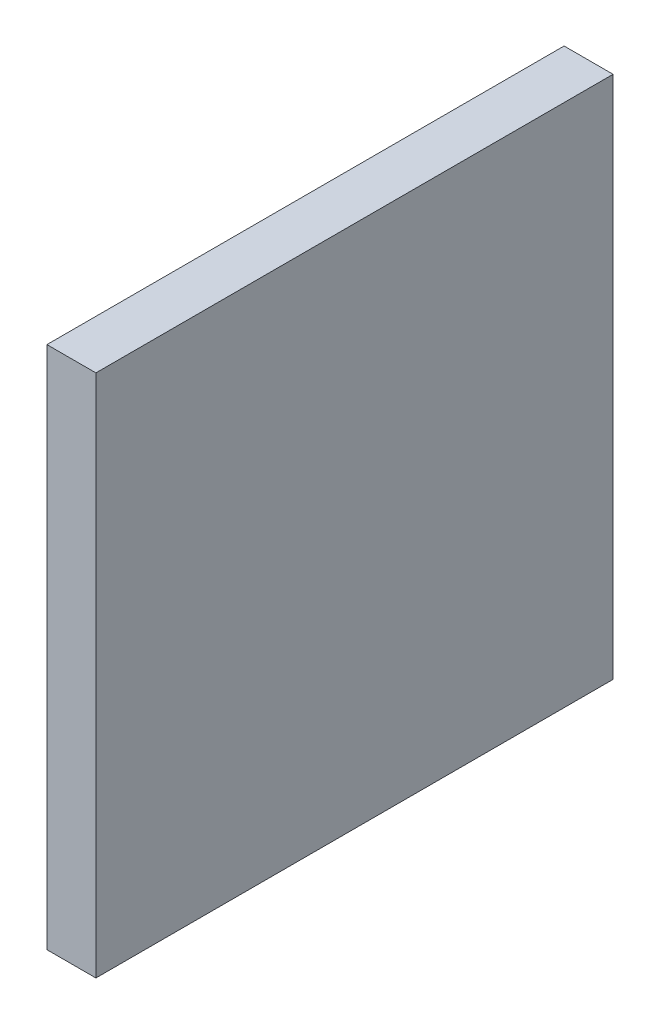
SolidWorks part; units mm, degrees
ref_plane "Front Plane" through (0, 0, 0) normal (0, 0, 1) x (1, 0, 0)
ref_plane "Top Plane" through (0, 0, 0) normal (0, 1, 0) x (1, 0, 0)
ref_plane "Right Plane" through (0, 0, 0) normal (1, 0, 0) x (0, 0, -1)
sketch "Sketch2" plane through (0, 0, -331.8) normal (0, 0, 1) x (1, 0, 0)
  line L0 (-122.3, 0) -> (-127.3, 0)
  line L1 (-122.3, 0) -> (-122.3, -53.5024)
  line L2 (-127.3, 0) -> (-127.3, -53.5024)
  line L3 (-122.3, -53.5024) -> (-127.3, -53.5024)
  line L4 (-249.6, 0) -> (0, 0) construction
  line L7 (-124.8, 0) -> (-124.8, -350.4) construction
  point P8 (-124.8, -53.5024)
  dimension "D1" = 5
extrude "Boss-Extrude1" add sketch "Sketch2" along normal up to surface (52.8 mm away)
